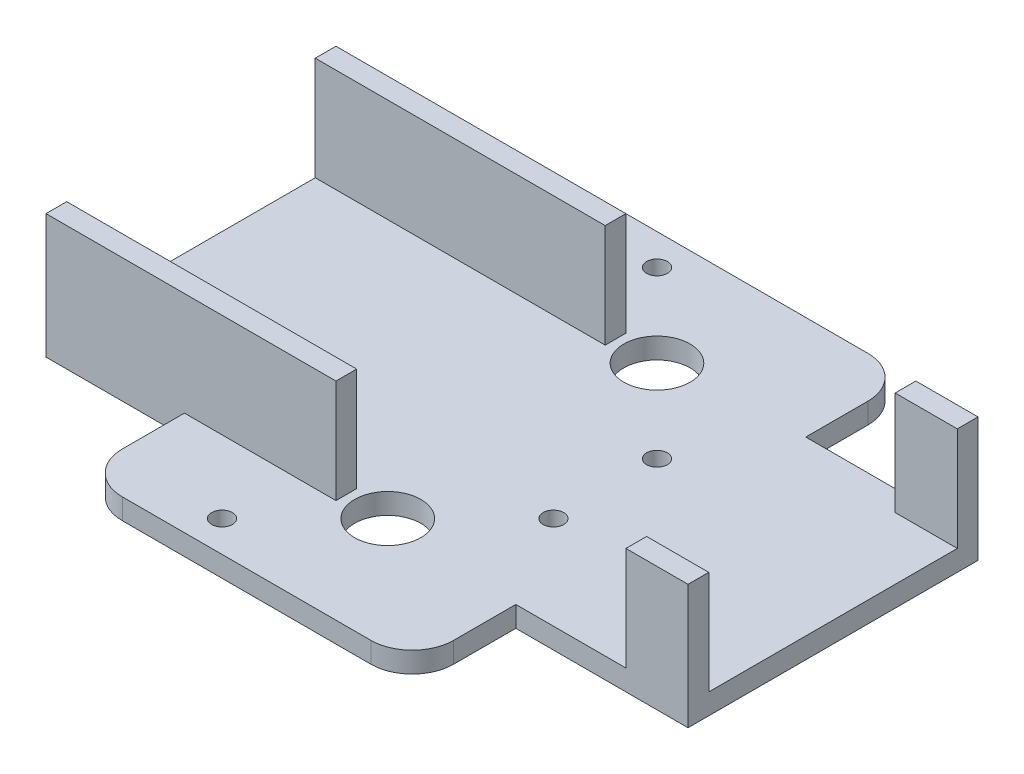
SolidWorks part; units mm, degrees
ref_plane "Front Plane" through (0, 0, 0) normal (0, 0, 1) x (1, 0, 0)
ref_plane "Top Plane" through (0, 0, 0) normal (0, 1, 0) x (1, 0, 0)
ref_plane "Right Plane" through (0, 0, 0) normal (1, 0, 0) x (0, 0, -1)
sketch "Sketch1" plane through (0, 0, 0) normal (0, 1, 0) x (1, 0, 0)
  line L0 (-100, 149.592) -> (-100, -127.6531) construction
  line L1 (-75, 35) -> (80, 35)
  line L2 (-75, 35) -> (-75, -35)
  line L3 (-75, -35) -> (80, -35)
  line L4 (80, 35) -> (80, -35)
  line L5 (-75, 35) -> (80, -35) construction
  line L6 (-75, -35) -> (80, 35) construction
  point P0 (2.5, 0)
  dimension "D1" = 180
  dimension "D2" = 70
  dimension "D3" = 25
extrude "Boss-Extrude1" add sketch "Sketch1" along normal blind 30
sketch "Sketch2" plane through (0, 0, 35) normal (0, 0, 1) x (1, 0, 0)
  line L0 (80, 30) -> (80, 0) construction
  line L5 (-75, 30) -> (80, 30) construction
  line L6 (-5, 30) -> (65, 30)
  line L7 (-5, 30) -> (-5, 5)
  line L8 (-5, 5) -> (65, 5)
  line L9 (65, 30) -> (65, 5)
  dimension "D1" = 70
  dimension "D2" = 25
  dimension "D3" = 15
extrude "Cut-Extrude1" cut sketch "Sketch2" against normal through all
sketch "Sketch5" plane through (80, 0, 0) normal (1, 0, 0) x (0, 0, -1)
  line L0 (-35, 30) -> (35, 30) construction
  line L1 (-30, 30) -> (30, 30)
  line L2 (-30, 30) -> (-30, 5)
  line L3 (-30, 5) -> (30, 5)
  line L4 (30, 30) -> (30, 5)
  line L5 (35, 30) -> (35, 0) construction
  dimension "D1" = 25
  dimension "D2" = 60
  dimension "D3" = 5
extrude "Cut-Extrude2" cut sketch "Sketch5" against normal through all
sketch "Sketch6" plane through (0, 0, 0) normal (0, 1, 0) x (1, 0, 0)
  line L0 (48.4211, 100.0199) -> (48.4211, -112.1239) construction
  line L5 (-124.3046, 0) -> (122.3185, 0) construction
  line L11 (-41.5789, -35) -> (38.4211, -35)
  line L12 (-41.5789, 60) -> (38.4211, 60)
  line L13 (-41.5789, 60) -> (-41.5789, 35)
  line L14 (-41.5789, 35) -> (38.4211, 35)
  line L15 (38.4211, 60) -> (38.4211, 35)
  line L16 (-41.5789, -35) -> (-41.5789, -60)
  line L17 (-41.5789, -60) -> (38.4211, -60)
  line L18 (38.4211, -35) -> (38.4211, -60)
  line L19 (-75, -35) -> (80, -35) construction
  line L20 (80, 35) -> (-75, 35) construction
  dimension "D1" = 10
  dimension "D2" = 10
  dimension "D3" = 90
  dimension "D4" = 90
  dimension "D5" = 25
  dimension "D6" = 25
extrude "Boss-Extrude2" add sketch "Sketch6" along normal blind 5
sketch "Sketch8" plane through (0, 5, 0) normal (0, 1, 0) x (1, 0, 0)
  line L0 (-78.836, 32.5) -> (81.5117, 32.5) construction
  line L1 (-78.836, -32.5) -> (87.6305, -32.5) construction
  line L2 (5, 92.4332) -> (5, -141.4934) construction
  line L3 (-5, 35) -> (-5, 30) construction
  line L4 (-5, 35) -> (-75, 35) construction
  line L7 (-75, -35) -> (-5, -35) construction
  circle A0 centre (5, 32.5) radius 8
  circle A1 centre (5, -32.5) radius 8
  circle A2 centre (-15, 52.5) radius 2.5
  circle A3 centre (25, 12.5) radius 2.5
  circle A4 centre (-15, -52.5) radius 2.5
  circle A5 centre (25, -12.5) radius 2.5
  dimension "D4" = 8
  dimension "D5" = 8
  dimension "D6" = 2.5
  dimension "D7" = 2.5
  dimension "D12" = 2.5
  dimension "D13" = 2.5
  dimension "D1" = 10
  dimension "D2" = 2.5
  dimension "D3" = 2.5
  dimension "D8" = 20
  dimension "D9" = 20
  dimension "D10" = 20
  dimension "D11" = 20
  dimension "D14" = 20
  dimension "D15" = 20
  dimension "D16" = 20
  dimension "D17" = 20
extrude "Cut-Extrude4" cut sketch "Sketch8" against normal through all
fillet "Fillet5" radius 10 1 edges at (38.4211, 2.5, 60)
fillet "Fillet6" radius 10 3 edges at (38.4211, 2.5, -60) (-41.5789, 2.5, -60) (-41.5789, 2.5, 60)
